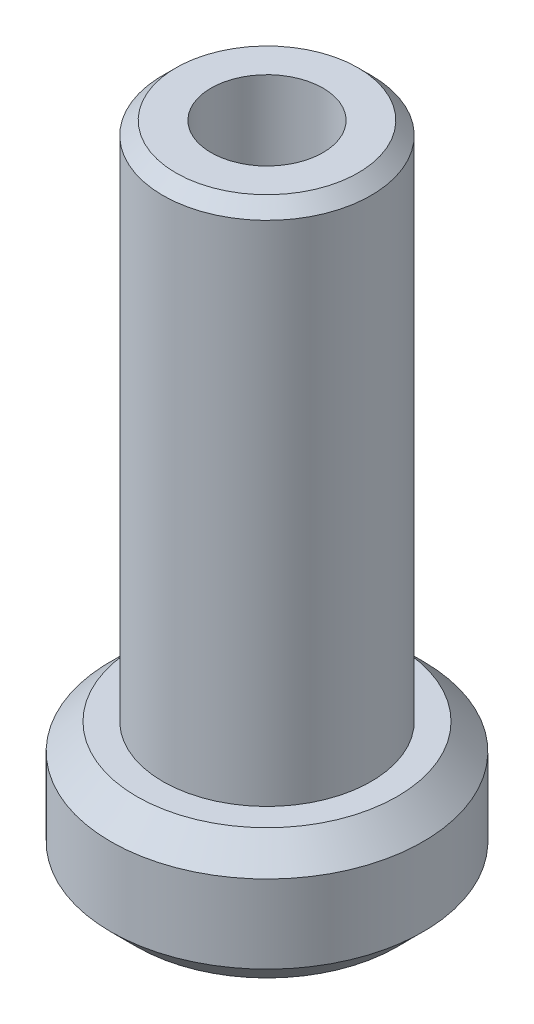
SolidWorks part; units mm, degrees
material "PUR"
ref_plane "Ebene vorne" through (0, 0, 0) normal (0, 0, 1) x (1, 0, 0)
ref_plane "Ebene oben" through (0, 0, 0) normal (0, 1, 0) x (1, 0, 0)
ref_plane "Ebene rechts" through (0, 0, 0) normal (1, 0, 0) x (0, 0, -1)
sketch "Skizze1" plane through (0, 0, 0) normal (0, 0, 1) x (1, 0, 0)
  line L0 (0, 0) -> (0, -6.8559) construction
  line L1 (0, 0) -> (0, 25)
  line L2 (0, 25) -> (-4, 25)
  line L3 (-4, 25) -> (-4, 5)
  line L4 (-4, 5) -> (-6, 5)
  line L5 (-6, 5) -> (-6, 0)
  line L6 (-6, 0) -> (0, 0)
  dimension "D1" = 8
  dimension "D2" = 20
  dimension "D3" = 5
  dimension "D4" = 12
revolve "Rotation1" add sketch "Skizze1" angle 360 about L0
hole_wizard "Stirnsenkung für M4 Zylinderschraube mit Innensechskant1" positions "Skizze2" profile "Skizze3" counterbore size "M4" standard "ISO" end condition through all
sketch "Skizze2" plane through (0, 0, 0) normal (0, -1, 0) x (-1, 0, 0)
  point P0 (0, 0)
sketch "Skizze3" plane through (0, 0, 0) normal (1, 0, 0) x (0, 0, -1)
  line L0 (0, 0) -> (0, 25)
  line L1 (0, 25) -> (2.15, 25)
  line L3 (2.15, 25) -> (2.15, 2)
  line L4 (2.15, 2) -> (4, 2)
  line L5 (4, 2) -> (4, 0)
  line L7 (4, 0) -> (0, 0)
  line L11 (0, -6.35) -> (0, 107.95) construction
  dimension "Bohrerdurchmesser" = 4.3
  dimension "Bohrungstiefe" = 25
  dimension "Senkdurchmesser2" = 8
  dimension "Senktiefe2" = 2
chamfer "Fase1" distance 1 angle 45 2 edges at (0, 5, 6) (0, 0, 6)
chamfer "Fase2" distance 0.5 angle 45 1 edges at (0, 25, 4)
